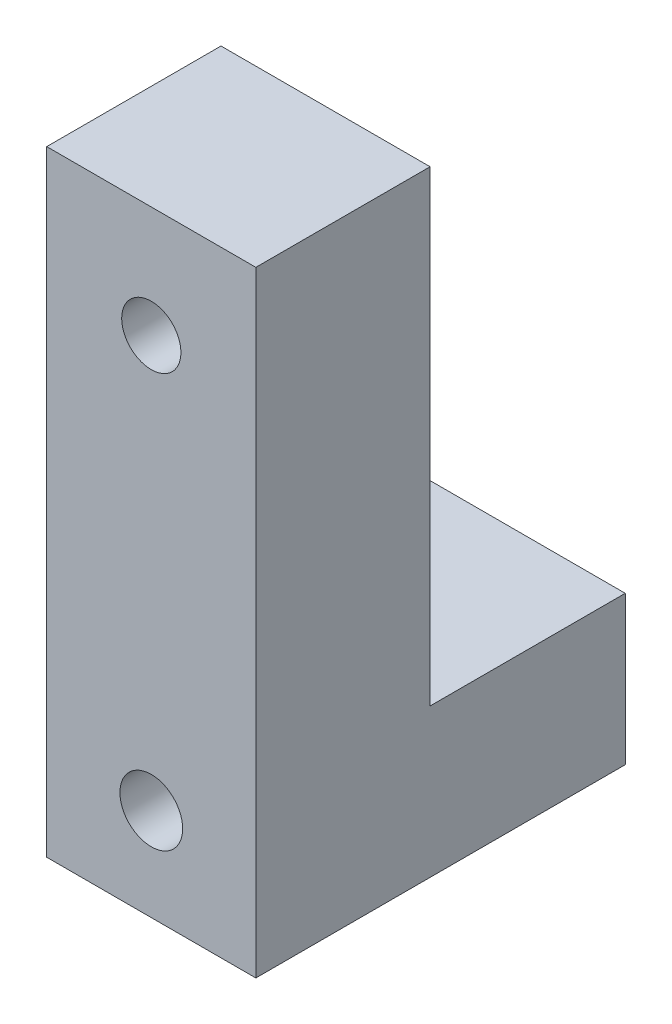
SolidWorks part; units mm, degrees
ref_plane "前视基准面" through (0, 0, 0) normal (0, 0, 1) x (1, 0, 0)
ref_plane "上视基准面" through (0, 0, 0) normal (0, 1, 0) x (1, 0, 0)
ref_plane "右视基准面" through (0, 0, 0) normal (1, 0, 0) x (0, 0, -1)
other "Configuration Table"
sketch "草图1" plane through (0, 0, 0) normal (1, 0, 0) x (0, 0, -1)
  line L6 (-18.5, 8) -> (-18.5, -13.3)
  line L8 (-46.5, 8) -> (-18.5, 8)
  line L19 (-71.5, 75) -> (-46.5, 75)
  line L20 (-18.5, -13.3) -> (-71.5, -13.3)
  line L21 (-46.5, 8) -> (-46.5, 75)
  line L24 (-71.5, -13.3) -> (-71.5, 75)
extrude "凸台-拉伸1" add sketch "草图1" along normal blind 30
sketch "草图2" plane through (0, 0, 18.5) normal (0, 0, -1) x (-1, 0, 0)
  circle A1 centre (-15, 0) radius 2.65
extrude "切除-拉伸1" cut sketch "草图2" against normal through all
ref_plane "基准面1" through (0, 0, 32.5) normal (0, 0, -1) x (-1, 0, 0)
sketch "草图4" plane through (0, 0, 32.5) normal (0, 0, -1) x (-1, 0, 0)
  circle A1 centre (-15, 0) radius 4.5
extrude "切除-拉伸3" cut sketch "草图4" against normal through all
sketch "草图5" plane through (0, 0, 46.5) normal (0, 0, -1) x (-1, 0, 0)
  circle A1 centre (-15, 59.0382) radius 4.25
extrude "切除-拉伸4" cut sketch "草图5" against normal through all
sketch "草图6" plane through (0, 0, 46.5) normal (0, 0, -1) x (-1, 0, 0)
  circle A2 centre (-15, 59.0382) radius 7
extrude "切除-拉伸5" cut sketch "草图6" against normal blind 8
